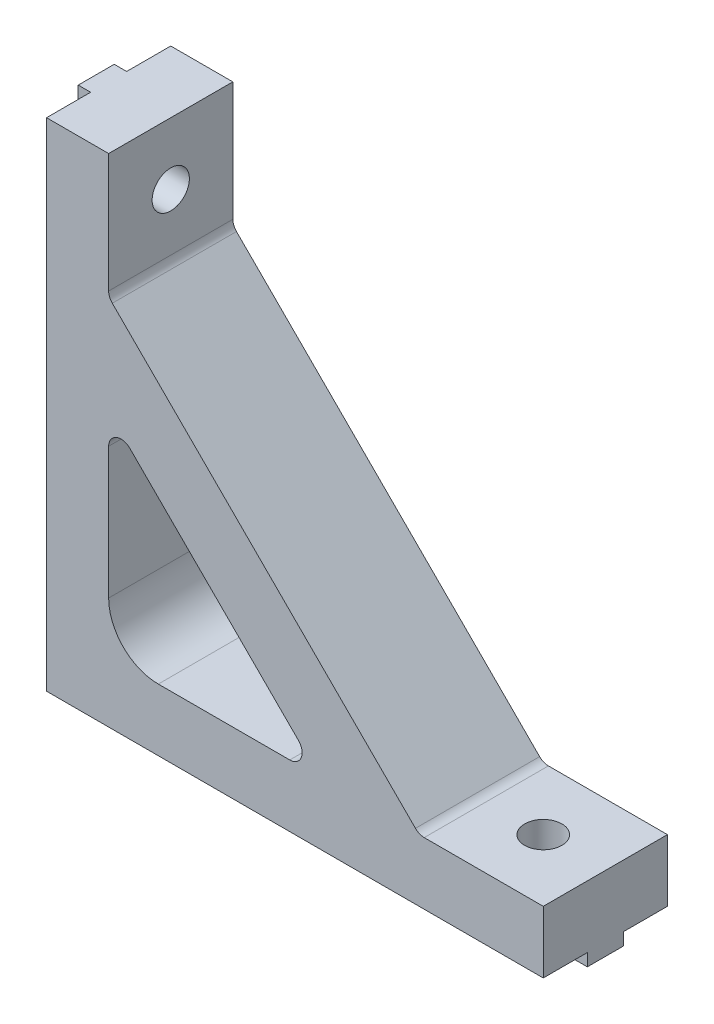
SolidWorks part; units mm, degrees
ref_plane "Front Plane" through (0, 0, 0) normal (0, 0, 1) x (1, 0, 0)
ref_plane "Top Plane" through (0, 0, 0) normal (0, 1, 0) x (1, 0, 0)
ref_plane "Right Plane" through (0, 0, 0) normal (1, 0, 0) x (0, 0, -1)
sketch "Esquisse1" plane through (0, 0, 0) normal (0, 0, 1) x (1, 0, 0)
  line L0 (0, 0) -> (40, 0)
  line L1 (40, 0) -> (40, 5)
  line L2 (40, 5) -> (9, 5)
  line L4 (5, 9) -> (5, 40)
  line L5 (5, 40) -> (0, 40)
  line L6 (0, 40) -> (0, 0)
  arc A0 (9, 5) -> (5, 9) centre (9, 9) cw
  dimension "D1" = 4
  dimension "D2" = 40
  dimension "D3" = 5
extrude "Main" add sketch "Esquisse1" along normal blind 10
sketch "Esquisse4" plane through (0, 0, 0) normal (-1, 0, 0) x (0, 0, 1)
  line L0 (10, 40) -> (0, 40) construction
  line L1 (3.55, 40) -> (6.45, 40)
  line L2 (3.55, 40) -> (3.55, 0)
  line L3 (3.55, 0) -> (6.45, 0)
  line L4 (6.45, 40) -> (6.45, 0)
  line L5 (10, 0) -> (0, 0) construction
  point P8 (5, 40)
  point P9 (5, 40)
  dimension "D1" = 2.9
extrude "MakerBeamFixVertical" add sketch "Esquisse4" along normal blind 1
sketch "Esquisse2" plane through (0, 0, 0) normal (-1, 0, 0) x (0, 0, 1)
  line L0 (10, 40) -> (6.45, 40) construction
  line L1 (10, 40) -> (0, 40) construction
  circle A0 centre (5, 35) radius 1.5
  point P9 (5, 40)
  dimension "D1" = 3
  dimension "D2" = 5
extrude "MakerBeamVerticalHole" cut sketch "Esquisse2" against normal through all both and the other way through all
sketch "Esquisse5" plane through (0, 0, 0) normal (0, -1, 0) x (-1, 0, 0)
  line L0 (-40, -10) -> (-40, 0) construction
  line L1 (0, -3.55) -> (-40, -3.55)
  line L2 (0, -3.55) -> (0, -6.45)
  line L3 (0, -6.45) -> (-40, -6.45)
  line L4 (-40, -3.55) -> (-40, -6.45)
  line L5 (1, -6.45) -> (0, -6.45) construction
extrude "MakerBeamFixHorizontal" add sketch "Esquisse5" along normal blind 1
sketch "Esquisse3" plane through (0, 0, 0) normal (0, -1, 0) x (1, 0, 0)
  line L0 (40, 10) -> (40, 6.45) construction
  line L1 (40, 10) -> (9, 10) construction
  circle A0 centre (35, 5) radius 1.5
  dimension "D1" = 5
  dimension "D2" = 5
  dimension "D3" = 3
extrude "MakerBeamHorizontalHole" cut sketch "Esquisse3" against normal through all both and the other way through all
sketch "Sketch2" plane through (0, 0, 10) normal (0, 0, 1) x (1, 0, 0)
  line L0 (5, 30) -> (30, 5)
  line L1 (5, 9) -> (5, 40) construction
  line L2 (40, 5) -> (9, 5) construction
  line L3 (5, 22) -> (22, 5)
  line L4 (5, 30) -> (5, 22)
  line L5 (22, 5) -> (30, 5)
  point P8 (5, 20.4519)
  dimension "D1" = 10
  dimension "D2" = 10
  dimension "D3" = 8
  dimension "D4" = 5.6569
extrude "Boss-Extrude1" add sketch "Sketch2" against normal blind 10
fillet "Fillet1" radius 1 4 edges at (5, 22, 5) (22, 5, 5) (5, 30, 5) (30, 5, 5)
